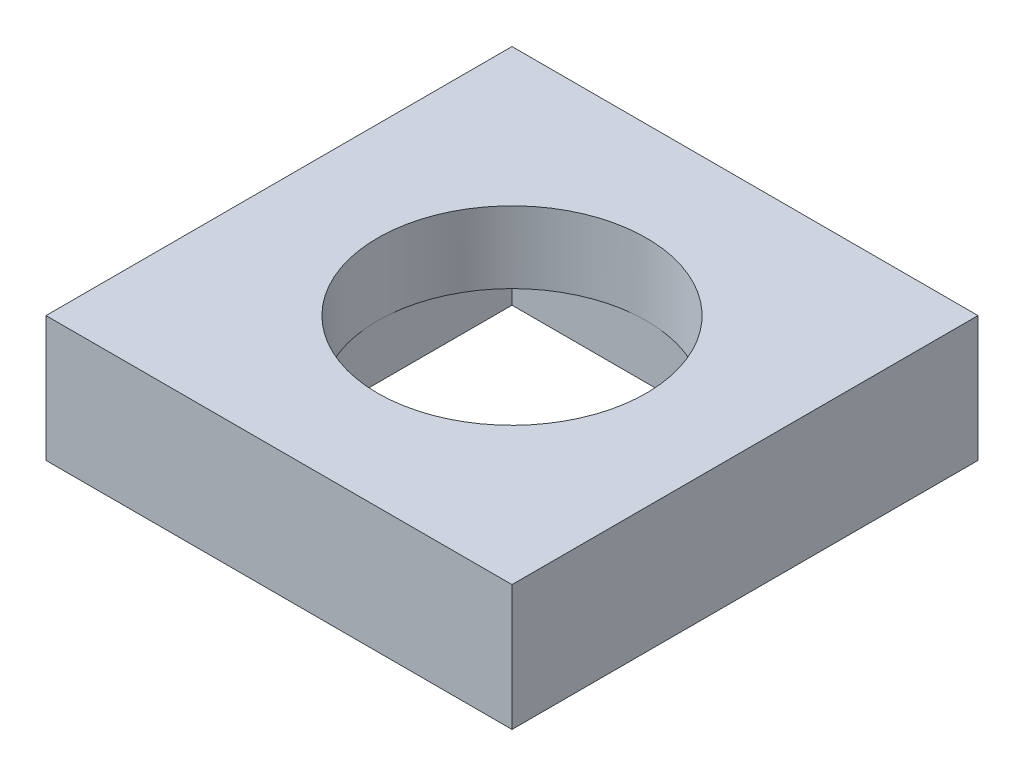
SolidWorks part; units mm, degrees
ref_plane "Front Plane" through (0, 0, 0) normal (0, 0, 1) x (1, 0, 0)
ref_plane "Top Plane" through (0, 0, 0) normal (0, 1, 0) x (1, 0, 0)
ref_plane "Right Plane" through (0, 0, 0) normal (1, 0, 0) x (0, 0, -1)
sketch "Sketch1" plane through (0, 0, 0) normal (0, 1, 0) x (1, 0, 0)
  line L1 (-1.6118, 0.5904) -> (0.9882, 0.5904)
  line L2 (-1.6118, 0.5904) -> (-1.6118, -2.0096)
  line L3 (-1.6118, -2.0096) -> (0.9882, -2.0096)
  line L4 (0.9882, 0.5904) -> (0.9882, -2.0096)
  circle A0 centre (-0.3118, -0.7096) radius 0.75
  point P6 (0, 0)
  dimension "D3" = 1.3
  dimension "D1" = 2.6
  dimension "D2" = 2.6
  dimension "D4" = 1.3
extrude "Boss-Extrude1" add sketch "Sketch1" along normal blind 0.7
sketch "Sketch2" plane through (0, 0, 0) normal (0, -1, 0) x (1, 0, 0)
  line L1 (-1.0618, 1.4596) -> (0.4382, 1.4596)
  line L2 (-1.0618, 1.4596) -> (-1.0618, -0.0404)
  line L3 (-1.0618, -0.0404) -> (0.4382, -0.0404)
  line L4 (0.4382, 1.4596) -> (0.4382, -0.0404)
  circle A0 centre (-0.3118, 0.7096) radius 0.75 construction
  dimension "D1" = 1.5
  dimension "D2" = 1.5
  dimension "D3" = 0.75
  dimension "D4" = 0.75
extrude "Cut-Extrude1" cut sketch "Sketch2" against normal blind 0.3
